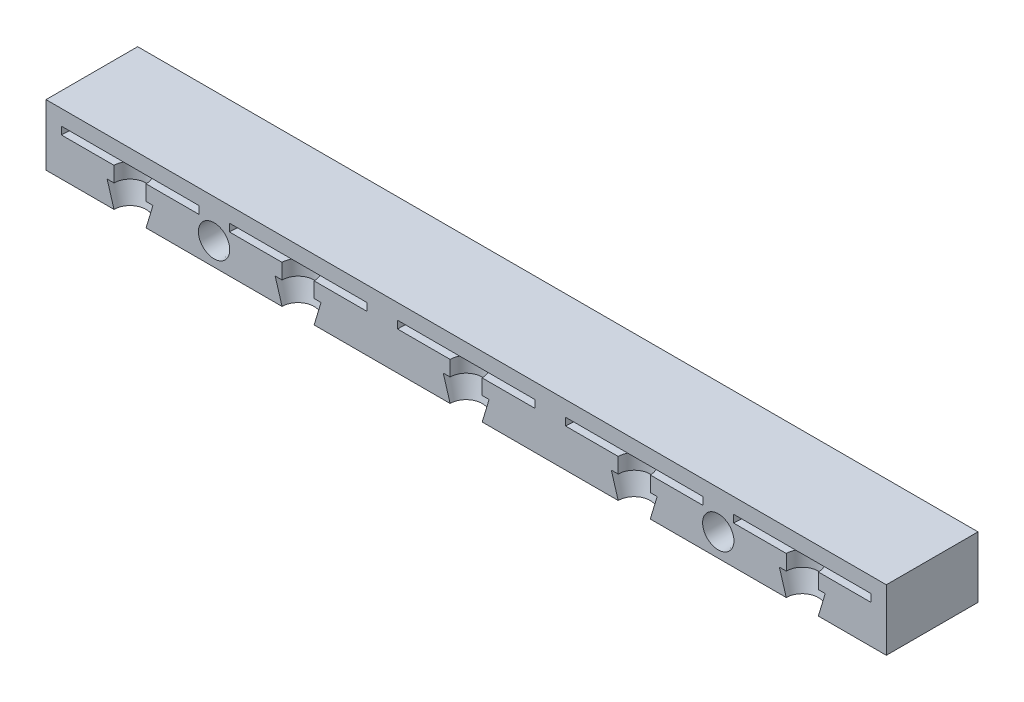
SolidWorks part; units mm, degrees
ref_plane "Front Plane" through (0, 0, 0) normal (0, 0, 1) x (1, 0, 0)
ref_plane "Top Plane" through (0, 0, 0) normal (0, 1, 0) x (1, 0, 0)
ref_plane "Right Plane" through (0, 0, 0) normal (1, 0, 0) x (0, 0, -1)
sketch "Sketch2" plane through (0, 0, 0) normal (0, 0, 1) x (1, 0, 0)
  line L1 (0, 0) -> (110, 0)
  line L2 (0, 0) -> (0, 8)
  line L3 (0, 8) -> (110, 8)
  line L4 (110, 0) -> (110, 8)
  dimension "D1" = 8
  dimension "D2" = 110
extrude "Boss-Extrude1" add sketch "Sketch2" against normal blind 12
sketch "Sketch3" plane through (0, 0, 0) normal (0, 0, 1) x (1, 0, 0)
  line L2 (8, 3) -> (8.9, 3)
  line L3 (8.9, 3) -> (8.9, 5)
  line L4 (8.9, 5) -> (2, 5)
  line L7 (11, 6) -> (11, 0) construction
  line L8 (8, 3) -> (8.9, 0)
  line L9 (8.9, 0) -> (11, 0)
  line L10 (0, 0) -> (110, 0) construction
  line L11 (11, 0) -> (11, 6)
  line L12 (2, 5) -> (2, 6)
  line L13 (2, 6) -> (11, 6)
  dimension "D1" = 2
  dimension "D2" = 0
  dimension "D3" = 2.1
  dimension "D4" = 3
  dimension "D5" = 1
  dimension "D6" = 3
  dimension "D7" = 2.1
  dimension "D8" = 0
revolve "Cut-Revolve1" cut sketch "Sketch3" angle 360 about L7
pattern_linear "LPattern1" count 5 spacing 22 along (1, 0, 0) of "Cut-Revolve1"
sketch "Sketch4" plane through (0, 0, 0) normal (0, 0, 1) x (1, 0, 0)
  line L0 (20, 8) -> (2, 8) construction
  line L1 (11, 0) -> (11, 8) construction
  line L2 (8.9, 0) -> (13.1, 0) construction
  line L3 (110, 0) -> (110, 8) construction
  line L4 (0, 0) -> (8.9, 0) construction
  line L7 (0, 0) -> (8.9, 0) construction
  circle A0 centre (22, 3) radius 2.05
  circle A2 centre (88, 3) radius 2.05
  dimension "D2" = 4.1
  dimension "D1" = 22
  dimension "D3" = 3
  dimension "D4" = 22
  dimension "D5" = 3
extrude "Cut-Extrude1" cut sketch "Sketch4" against normal blind 5 draft 1
equation "\"D4@Sketch4\"=\"D1@Sketch4\""
equation "\"D5@Sketch4\"=\"D3@Sketch4\""
